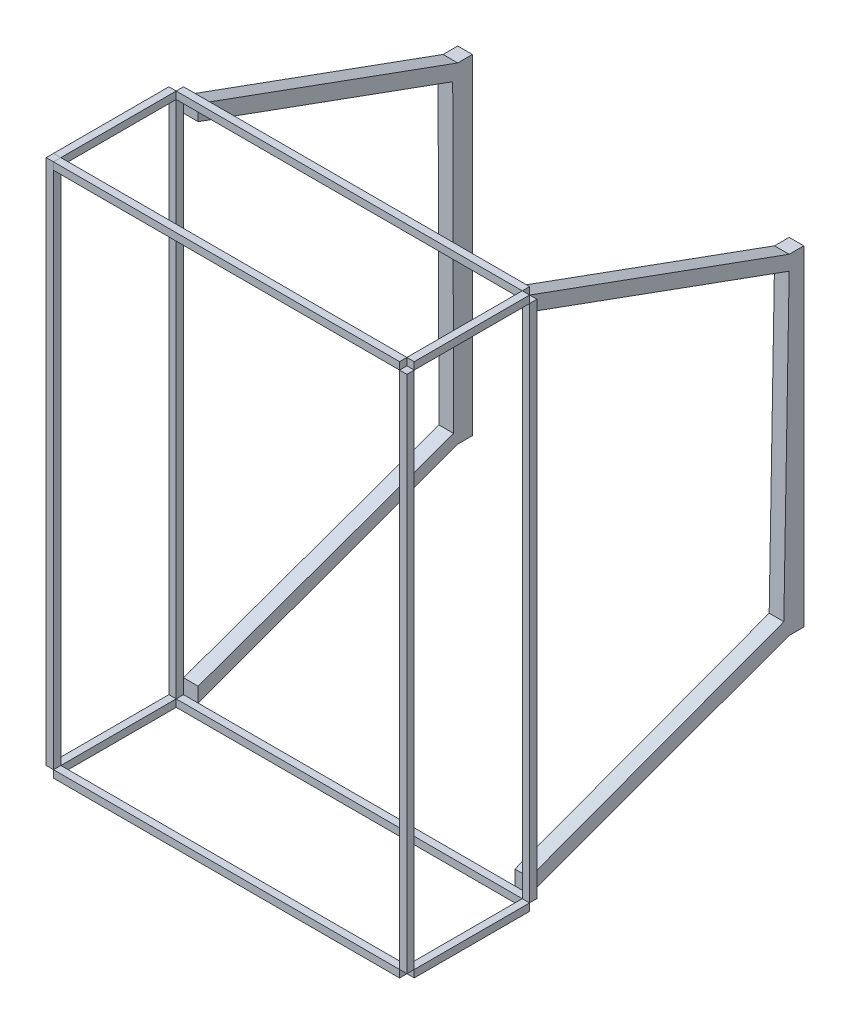
SolidWorks part; units mm, degrees
ref_plane "Front Plane" through (0, 0, 0) normal (0, 0, 1) x (1, 0, 0)
ref_plane "Top Plane" through (0, 0, 0) normal (0, 1, 0) x (1, 0, 0)
ref_plane "Right Plane" through (0, 0, 0) normal (1, 0, 0) x (0, 0, -1)
sketch "Sketch1" plane through (0, 0, 0) normal (0, 0, 1) x (1, 0, 0)
  line L1 (0, 0) -> (6.35, 0)
  line L2 (0, 0) -> (0, 6.35)
  line L3 (0, 6.35) -> (6.35, 6.35)
  line L4 (6.35, 0) -> (6.35, 6.35)
  dimension "D1" = 6.35
  dimension "D2" = 6.35
extrude "Boss-Extrude1" add sketch "Sketch1" along normal blind 100 contours L3 L4 L1 L2
ref_plane "Plane1" through (0, 0, 100) normal (1, 0, 0) x (0, 0, -1)
sketch "Sketch4" plane through (0, 0, 0) normal (0, -1, 0) x (-1, 0, 0)
  line L1 (0, -106.35) -> (-6.35, -106.35)
  line L2 (0, -106.35) -> (0, -100)
  line L3 (0, -100) -> (-6.35, -100)
  line L4 (-6.35, -106.35) -> (-6.35, -100)
  dimension "D1" = 6.35
extrude "Boss-Extrude3" add sketch "Sketch4" along normal blind 450 and the other way up to vertex (6.35 mm away) separate body contours L1 L4 L3 L2 other way up to point (0, 6.35, 100)
sketch "Sketch6" plane through (0, 0, 100) normal (0, 0, -1) x (-1, 0, 0)
  line L1 (-6.35, -450) -> (0, -450)
  line L2 (-6.35, -450) -> (-6.35, -456.3788)
  line L3 (-6.35, -456.3788) -> (0, -456.3788)
  line L4 (0, -450) -> (0, -456.3788)
extrude "Boss-Extrude4" add sketch "Sketch6" along normal blind 100 separate body contours L4 L3 L2 L1
sketch "Sketch7" plane through (6.35, 0, 0) normal (1, 0, 0) x (0, 0, -1)
  line L0 (-100, 0) -> (0, 0) construction
  line L1 (-106.35, 0) -> (-100, 0)
  line L2 (-106.35, 0) -> (-106.35, 6.35)
  line L3 (-106.35, 6.35) -> (-100, 6.35)
  line L4 (-100, 0) -> (-100, 6.35)
extrude "Boss-Extrude5" add sketch "Sketch7" along normal blind 300 separate body contours L3 L4 L1 L2
sketch "Sketch8" plane through (6.35, 0, 0) normal (1, 0, 0) x (0, 0, -1)
  line L1 (-106.35, -450) -> (-100, -450)
  line L2 (-106.35, -450) -> (-106.35, -456.3788)
  line L3 (-106.35, -456.3788) -> (-100, -456.3788)
  line L4 (-100, -450) -> (-100, -456.3788)
extrude "Boss-Extrude6" add sketch "Sketch8" along normal blind 300 separate body
sketch "Sketch10" plane through (0, -450, 0) normal (0, 1, 0) x (1, 0, 0)
  line L1 (306.35, -100) -> (312.7, -100)
  line L2 (306.35, -100) -> (306.35, -106.35)
  line L3 (306.35, -106.35) -> (312.7, -106.35)
  line L4 (312.7, -100) -> (312.7, -106.35)
  dimension "D1" = 6.35
  dimension "D2" = 6.35
extrude "Boss-Extrude7" add sketch "Sketch10" along normal blind 450 separate body contours L1 L4 L3 L2
sketch "Sketch12" plane through (0, 0, 0) normal (0, -1, 0) x (-1, 0, 0)
  line L1 (0, 0) -> (-6.35, 0)
  line L2 (0, 0) -> (0, 6.35)
  line L3 (0, 6.35) -> (-6.35, 6.35)
  line L4 (-6.35, 0) -> (-6.35, 6.35)
  dimension "D1" = 6.35
  dimension "D2" = 6.35
extrude "Boss-Extrude8" add sketch "Sketch12" along normal blind 450 separate body contours L2 L3 L4 L1
sketch "Sketch16" plane through (0, 0, 100) normal (0, 0, -1) x (-1, 0, 0)
  line L1 (-306.35, -450) -> (-312.7, -450)
  line L2 (-306.35, -450) -> (-306.35, -456.35)
  line L3 (-306.35, -456.35) -> (-312.7, -456.35)
  line L4 (-312.7, -450) -> (-312.7, -456.35)
  line L5 (-306.35, 0) -> (-312.7, 0)
  line L6 (-306.35, 0) -> (-306.35, 6.4147)
  line L7 (-306.35, 6.4147) -> (-312.7, 6.4147)
  line L8 (-312.7, 0) -> (-312.7, 6.4147)
  dimension "D1" = 6.35
  dimension "D2" = 6.35
extrude "Boss-Extrude9" add sketch "Sketch16" along normal blind 100 separate body contours L3 L4 L1 L2
ref_plane "Plane2" through (312.7, 0, 100) normal (1, 0, 0) x (0, 0, -1)
ref_plane "Plane3" through (312.7, 0, 100) normal (0, -1, 0) x (-1, 0, 0)
sketch "Sketch20" plane through (0, 0, 100) normal (0, 0, -1) x (-1, 0, 0)
  line L0 (-436.45, 0) -> (-188.95, 0) construction
  line L1 (-306.35, 6.35) -> (-312.7, 6.35)
  line L2 (-306.35, 6.35) -> (-306.35, 0)
  line L3 (-306.35, 0) -> (-312.7, 0)
  line L4 (-312.7, 6.35) -> (-312.7, 0)
  line L5 (-312.7, 1.7463) -> (-312.7, -1.7463) construction
extrude "Boss-Extrude10" add sketch "Sketch20" along normal blind 100 separate body contours L1 L4 L3 L2
sketch "Sketch21" plane through (6.35, 0, 0) normal (1, 0, 0) x (0, 0, -1)
  line L0 (0, -450) -> (0, -456.3788) construction
  line L1 (6.35, -450) -> (0, -450)
  line L2 (6.35, -450) -> (6.35, -456.3788)
  line L3 (6.35, -456.3788) -> (0, -456.3788)
  line L4 (0, -450) -> (0, -456.3788)
extrude "Boss-Extrude11" add sketch "Sketch21" along normal blind 300 separate body contours L2 L3 L4 L1
sketch "Sketch22" plane through (0, -450, 0) normal (0, 1, 0) x (1, 0, 0)
  line L1 (312.7, 0) -> (306.35, 0)
  line L2 (312.7, 0) -> (312.7, 6.35)
  line L3 (312.7, 6.35) -> (306.35, 6.35)
  line L4 (306.35, 0) -> (306.35, 6.35)
extrude "Boss-Extrude12" add sketch "Sketch22" along normal blind 450 separate body
sketch "Sketch23" plane through (306.35, 0, 0) normal (-1, 0, 0) x (0, 0, 1)
  line L0 (0, 6.35) -> (0, 0) construction
  line L1 (-6.35, 0) -> (0, 0)
  line L2 (-6.35, 0) -> (-6.35, 6.35)
  line L3 (-6.35, 6.35) -> (0, 6.35)
  line L4 (0, 0) -> (0, 6.35)
extrude "Boss-Extrude13" add sketch "Sketch23" along normal blind 300 separate body
sketch "Sketch24" plane through (0, -456.35, 0) normal (0, -1, 0) x (1, 0, 0)
  line L0 (6.35, 0) -> (6.35, 100) construction
  line L1 (0, 0) -> (0, 100) construction
  line L2 (6.35, 0) -> (6.35, 100)
  line L3 (0, 0) -> (0, 100)
  line L8 (6.35, 100) -> (0, 100)
  line L9 (0, 100) -> (0, 0)
  line L10 (0, 0) -> (6.35, 0)
  line L11 (6.35, 0) -> (6.35, 100)
  line L12 (6.35, 100) -> (0, 100)
  line L13 (0, 100) -> (0, 0)
  line L14 (0, 0) -> (6.35, 0)
  line L15 (6.35, 0) -> (6.35, 100)
  dimension "D1" = 0
sketch "Sketch25" plane through (6.35, 0, 0) normal (1, 0, 0) x (0, 0, -1)
  line L0 (6.35, 0) -> (231.35, -81.8933)
  line L1 (231.35, -81.8933) -> (227.0063, -93.8274)
  line L2 (227.0063, -93.8274) -> (6.35, -13.5151)
  line L3 (6.35, -450) -> (6.35, 0) construction
  line L4 (6.35, -13.5151) -> (6.35, 0)
  dimension "D1" = 12.7
  dimension "D2" = 70
  dimension "D3" = 225
extrude "Boss-Extrude20" add sketch "Sketch25" along normal blind 12.7 separate body contours L2 L4 L0 L1
sketch "Sketch26" plane through (306.35, 0, 0) normal (-1, 0, 0) x (0, 0, 1)
  line L0 (-6.35, 0) -> (-231.35, -81.8933)
  line L1 (-231.35, -81.8933) -> (-231.35, -94.5933)
  line L2 (-231.35, -94.5933) -> (-6.35, -12.7)
  line L3 (-6.35, 0) -> (-6.35, -450) construction
  line L4 (-6.35, -12.7) -> (-6.35, 0)
  dimension "D1" = 12.7
  dimension "D2" = 12.7
  dimension "D3" = 70
  dimension "D4" = 225
extrude "Boss-Extrude21" add sketch "Sketch26" along normal blind 12.7 separate body
sketch "Sketch27" plane through (306.35, 0, 0) normal (-1, 0, 0) x (0, 0, 1)
  line L0 (-6.35, -450) -> (-231.35, -368.1067)
  line L1 (-231.35, -368.1067) -> (-226.7276, -355.4067)
  line L2 (-226.7276, -355.4067) -> (-6.35, -437.3)
  line L3 (-6.35, 0) -> (-6.35, -450) construction
  line L4 (-6.35, -437.3) -> (-6.35, -450)
  dimension "D1" = 12.7
  dimension "D2" = 12.7
  dimension "D3" = 70
  dimension "D4" = 225
extrude "Boss-Extrude22" add sketch "Sketch27" along normal blind 12.7 separate body
sketch "Sketch28" plane through (6.35, 0, 0) normal (1, 0, 0) x (0, 0, -1)
  line L0 (6.35, -450) -> (231.35, -368.1067)
  line L1 (231.35, -368.1067) -> (227.7608, -358.2453)
  line L2 (227.7608, -358.2453) -> (6.35, -437.3)
  line L3 (6.35, -450) -> (6.35, 0) construction
  line L4 (6.35, -437.3) -> (6.35, -450)
  dimension "D1" = 70
  dimension "D2" = 12.7
  dimension "D3" = 225
extrude "Boss-Extrude23" add sketch "Sketch28" along normal blind 12.7 separate body
sketch "Sketch29" plane through (306.35, 0, 0) normal (1, 0, 0) x (0, 0, -1)
  line L0 (231.35, -81.8933) -> (231.35, -94.5933)
  line L1 (231.35, -94.5933) -> (226.7276, -355.4067)
  line L2 (226.7276, -355.4067) -> (231.35, -368.1067)
  line L3 (231.35, -368.1067) -> (244.05, -368.1067)
  line L4 (244.05, -368.1067) -> (244.05, -81.8933)
  line L5 (244.05, -81.8933) -> (231.35, -81.8933)
  dimension "D1" = 12.7
extrude "Boss-Extrude24" add sketch "Sketch29" against normal blind 12.7
sketch "Sketch31" plane through (6.35, 0, 0) normal (-1, 0, 0) x (0, 0, 1)
  line L0 (-231.35, -81.8933) -> (-227.0063, -93.8274)
  line L1 (-231.35, -81.8933) -> (-227.0063, -93.8274) construction
  line L2 (-227.0063, -93.8274) -> (-227.7608, -358.2453)
  line L3 (-227.7608, -358.2453) -> (-231.35, -368.1067)
  line L4 (-231.35, -368.1067) -> (-244.05, -368.1067)
  line L5 (-244.05, -368.1067) -> (-244.05, -81.8933)
  line L6 (-244.05, -81.8933) -> (-231.35, -81.8933)
extrude "Boss-Extrude25" add sketch "Sketch31" against normal blind 12.7
